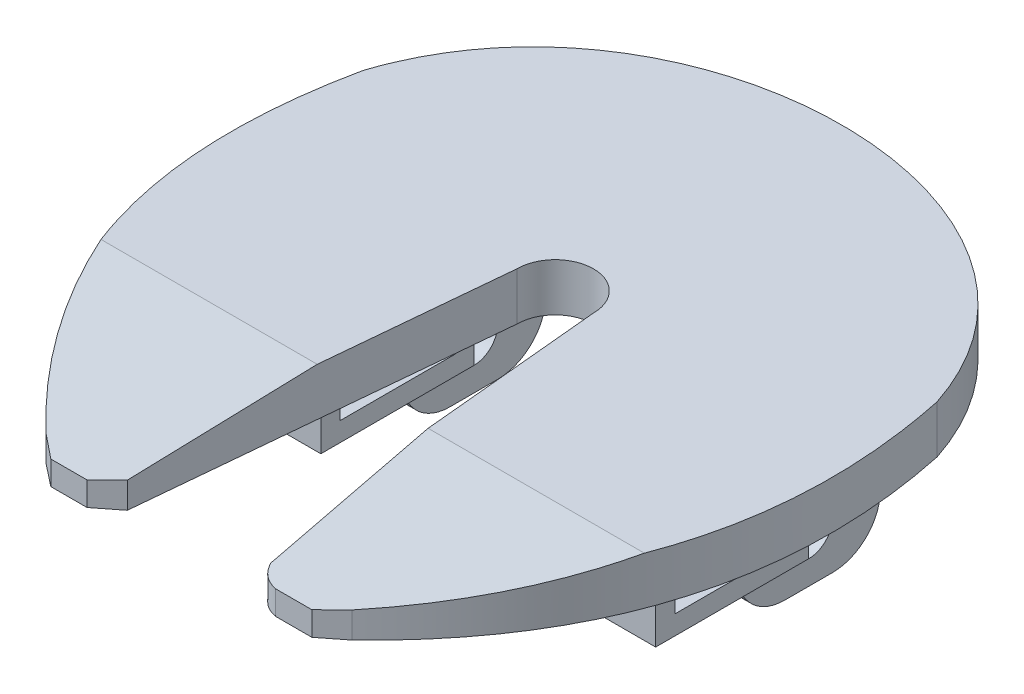
SolidWorks part; units mm, degrees
ref_plane "Front Plane" through (0, 0, 0) normal (0, 0, 1) x (1, 0, 0)
ref_plane "Top Plane" through (0, 0, 0) normal (0, 1, 0) x (1, 0, 0)
ref_plane "Right Plane" through (0, 0, 0) normal (1, 0, 0) x (0, 0, -1)
sketch "Sketch1" plane through (0, 0, 0) normal (0, 1, 0) x (1, 0, 0)
  line L0 (0, 0) -> (60, 0) construction
  line L1 (30, 0) -> (30, -55.8961) construction
  line L2 (26, -9.9147) -> (22.5, -47.1464)
  line L3 (34, -9.9147) -> (37.5, -47.1464)
  line L4 (14, -47.1464) -> (16.3589, -49)
  line L5 (16.3589, -49) -> (20.1411, -49)
  line L6 (20.1411, -49) -> (22.5, -47.1464)
  line L8 (39.8589, -49) -> (43.6411, -49)
  line L9 (43.6411, -49) -> (46, -47.1464)
  line L10 (26, -9.9147) -> (50026, -9.9147) construction
  arc A0 (34, -9.9147) -> (26, -9.9147) centre (30, -9.9147) ccw
  spline S0 degree 3 poles (0, 0) (8.75, 26.7804) (51.25, 26.7804) (60, 0) knots 0 0 0 0 1 1 1 1
  spline S1 degree 2 poles (0, 0) (-5.9385, -28.1192) (14, -47.1464) knots 0 0 0 1 1 1
  spline S2 degree 2 poles (60, 0) (65.9385, -28.1192) (46, -47.1464) knots 0 0 0 1 1 1
  spline S3 degree 2 poles (37.5, -47.1464) (38.1969, -48.6873) (39.8589, -49) knots 0 0 0 1 1 1
  point P11 (30, 0)
  point P12 (30, 20.0853)
  dimension "D13" = 8
  dimension "D1" = 25
  dimension "D2" = 60
  dimension "D3" = 25
  dimension "D4" = 25
  dimension "D5" = 30
  dimension "D6" = 30
  dimension "D7" = 21
  dimension "D8" = 21
  dimension "D9" = 65
  dimension "D10" = 16
  dimension "D11" = 16
  dimension "D12" = 30
  dimension "D14" = 3
  dimension "D15" = 3
  dimension "D16" = 3
  dimension "D17" = 3
  dimension "D18" = 7.5
  dimension "D19" = 7.5
  dimension "D20" = 1.55
  dimension "D21" = 1.55
  dimension "D22" = 49
extrude "Boss-Extrude1" add sketch "Sketch1" along normal blind 5
sketch "Sketch2" plane through (0, 0, 0) normal (0, -1, 0) x (1, 0, 0)
  line L0 (30, 5.9147) -> (30, 12.9147) construction
  line L1 (30, 12.9147) -> (-49970, 12.9147) construction
  line L2 (30, 24.9147) -> (17.9181, 24.9147) construction
  line L3 (57.5, 12.9147) -> (37.5, 12.9147)
  line L4 (57.5, 24.9147) -> (37.5, 24.9147)
  line L5 (22.5, 12.9147) -> (2.5, 12.9147)
  line L6 (22.5, 24.9147) -> (2.5, 24.9147)
  line L7 (57.5, 10.9147) -> (37.5, 10.9147)
  line L8 (22.5, 10.9147) -> (2.5, 10.9147)
  line L9 (57.5, 26.9147) -> (37.5, 26.9147)
  line L10 (22.5, 26.9147) -> (2.5, 26.9147)
  line L11 (57.5, 10.9147) -> (57.5, 12.9147)
  line L12 (37.5, 10.9147) -> (37.5, 12.9147)
  line L13 (2.5, 10.9147) -> (2.5, 12.9147)
  line L14 (22.5, 10.9147) -> (22.5, 12.9147)
  line L15 (2.5, 24.9147) -> (2.5, 26.9147)
  line L16 (22.5, 24.9147) -> (22.5, 26.9147)
  line L17 (37.5, 24.9147) -> (37.5, 26.9147)
  line L18 (57.5, 24.9147) -> (57.5, 26.9147)
  arc A0 (26, 9.9147) -> (34, 9.9147) centre (30, 9.9147) ccw construction
  dimension "D1" = 7
  dimension "D2" = 12
  dimension "D3" = 20
  dimension "D4" = 15
  dimension "D5" = 7.5
  dimension "D6" = 2
  dimension "D7" = 2
extrude "Boss-Extrude2" add sketch "Sketch2" along normal blind 3
sketch "Sketch3" plane through (0, -3, 0) normal (0, -1, 0) x (1, 0, 0)
  line L0 (57.5, 10.9147) -> (37.5, 10.9147)
  line L1 (37.5, 10.9147) -> (37.5, 26.9147)
  line L2 (37.5, 26.9147) -> (57.5, 26.9147)
  line L3 (57.5, 26.9147) -> (57.5, 10.9147)
  line L4 (22.5, 10.9147) -> (2.5, 10.9147)
  line L5 (2.5, 10.9147) -> (2.5, 26.9147)
  line L6 (2.5, 26.9147) -> (22.5, 26.9147)
  line L7 (22.5, 26.9147) -> (22.5, 10.9147)
extrude "Boss-Extrude3" add sketch "Sketch3" along normal blind 2
sketch "Sketch5" plane through (0, 0, 0) normal (1, 0, 0) x (0, 0, -1)
  line L0 (-29, 5) -> (-49, 2.5)
  line L1 (0, 5) -> (-47.1464, 5) construction
  line L2 (-49, 5) -> (-49, 0) construction
  line L3 (-49, 2.5) -> (-49, 5)
  line L4 (-49, 5) -> (-29, 5)
  dimension "D1" = 20
extrude "Cut-Extrude1" cut sketch "Sketch5" along normal through all
sketch "Sketch6" plane through (0, 0, 0) normal (0, -1, 0) x (1, 0, 0)
  line L0 (10, 10.9147) -> (10, -4.0853)
  line L1 (10, -4.0853) -> (15, -4.0853)
  line L2 (15, -4.0853) -> (15, 10.9147)
  line L3 (15, 10.9147) -> (10, 10.9147)
  line L4 (2.5, 10.9147) -> (22.5, 10.9147) construction
  point P6 (12.5, 10.9147)
  point P7 (12.5, 10.9147)
  dimension "D1" = 15
  dimension "D2" = 5
extrude "Boss-Extrude4" add sketch "Sketch6" along normal blind 15
ref_plane "Plane1" through (30, 0, 0) normal (1, 0, 0) x (0, 0, -1)
mirror "Mirror1" about plane through (30, 0, 0) normal (1, 0, 0) of "Boss-Extrude4"
sketch "Sketch7" plane through (10, 0, 0) normal (-1, 0, 0) x (0, 0, 1)
  line L0 (0, 0) -> (47.1464, 0) construction
  line L1 (10.9147, -15) -> (-4.0853, -15) construction
  circle A0 centre (3.4147, -10) radius 2.5
  point P8 (3.4147, -15)
  dimension "D1" = 5
  dimension "D2" = 10
extrude "Cut-Extrude2" cut sketch "Sketch7" against normal up to surface (40 mm away) up to face at (50, -7, 4.9147)
fillet "Fillet1" radius 5 4 edges at (12.5, -15, -4.0853) (12.5, -15, 10.9147) (47.5, -15, 10.9147) (47.5, -15, -4.0853)
sketch "Sketch8" plane through (0, 0, 0) normal (0, -1, 0) x (1, 0, 0)
  line L0 (2.5, 12.9147) -> (2.5, 24.9147)
  line L1 (2.5, 24.9147) -> (4.5, 24.9147)
  line L2 (2.5, 24.9147) -> (22.5, 24.9147) construction
  line L3 (4.5, 24.9147) -> (4.5, 12.9147)
  line L4 (4.5, 12.9147) -> (2.5, 12.9147)
  dimension "D1" = 2
extrude "Boss-Extrude5" add sketch "Sketch8" along normal up to surface (3 mm away) up to face at (12.5, -3, 18.9147)
